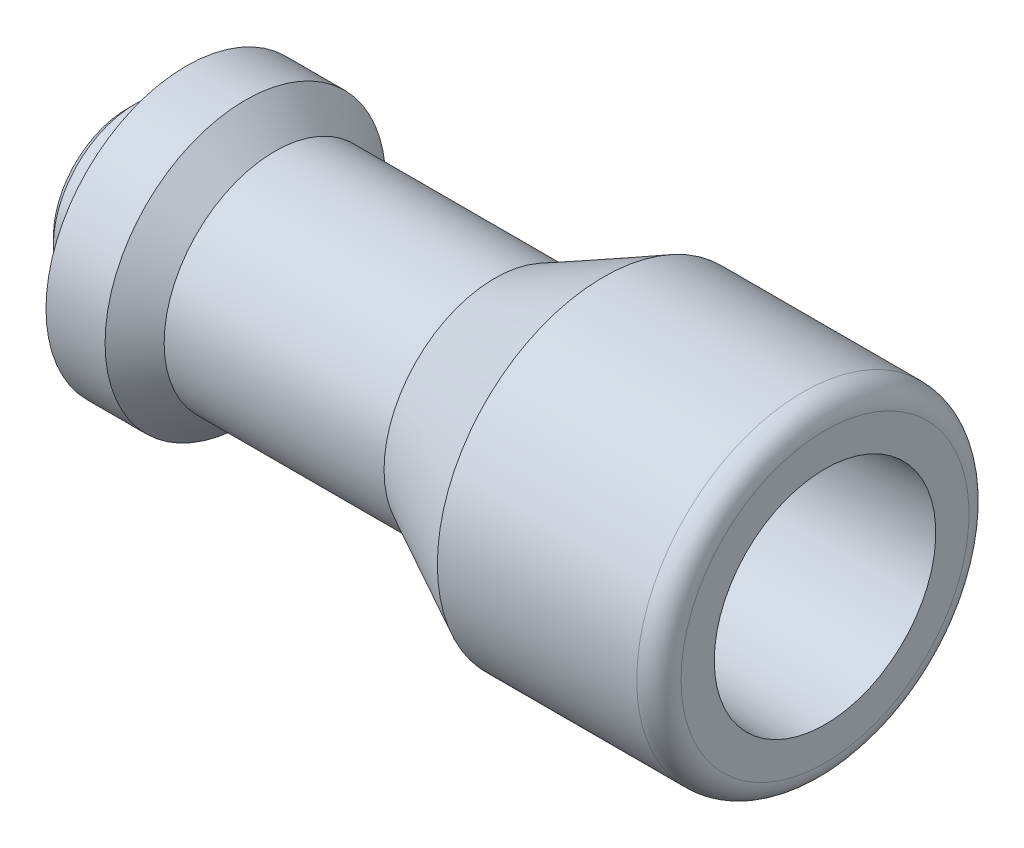
SolidWorks part; units mm, degrees
ref_plane "Plane1" through (0, 0, 0) normal (0, 0, 1) x (1, 0, 0)
ref_plane "Plane2" through (0, 0, 0) normal (0, 1, 0) x (1, 0, 0)
ref_plane "Plane3" through (0, 0, 0) normal (1, 0, 0) x (0, 0, -1)
sketch "Sketch1" plane through (0, 0, 0) normal (0, 0, 1) x (1, 0, 0)
  line L0 (0, 0) -> (150, 0) construction
  line L1 (44.5, 5.1) -> (41.5555, 0)
  line L2 (0, 0) -> (41.5555, 0)
  line L3 (94.5, 15) -> (94.5, 19.5)
  line L4 (91.5, 22.5) -> (64.5, 22.5)
  line L5 (8, 19) -> (8, 11)
  line L6 (8, 11) -> (1, 11)
  line L7 (0, 10) -> (0, 0)
  line L8 (66.5, 13.2497) -> (66.5, 5.1)
  line L9 (67.2721, 14.0492) -> (94.5, 15)
  line L10 (44.5, 5.1) -> (66.5, 5.1)
  line L12 (0, 10) -> (1, 11)
  line L13 (64.5, 22.5) -> (49.7804, 15)
  line L14 (49.7804, 15) -> (20, 15)
  line L15 (20, 15) -> (16, 19)
  line L16 (16, 19) -> (8, 19)
  arc A0 (94.5, 19.5) -> (91.5, 22.5) centre (91.5, 19.5) ccw
  arc A1 (67.2721, 14.0492) -> (66.5, 13.2497) centre (67.3, 13.2497) ccw
  dimension "D11" = 3
  dimension "D16" = 0.8
  dimension "D3" = 22
  dimension "D4" = 45
  dimension "D5" = 28
  dimension "D6" = 30
  dimension "D7" = 94.5
  dimension "D8" = 2
  dimension "D9" = 60
  dimension "D10" = 10.2
  dimension "D12" = 30
  dimension "D13" = 1
  dimension "D14" = 22
  dimension "D15" = 8
  dimension "D17" = 45
  dimension "D18" = 8
  dimension "D19" = 30
  dimension "D20" = 8
  dimension "D21" = 45
  dimension "D22" = 27
  dimension "D23" = 38
revolve "Revolve1" add sketch "Sketch1" angle 360 about L0
cosmetic thread "Cosmetic Thread1" parameters "D1"=18, "D2"=12
